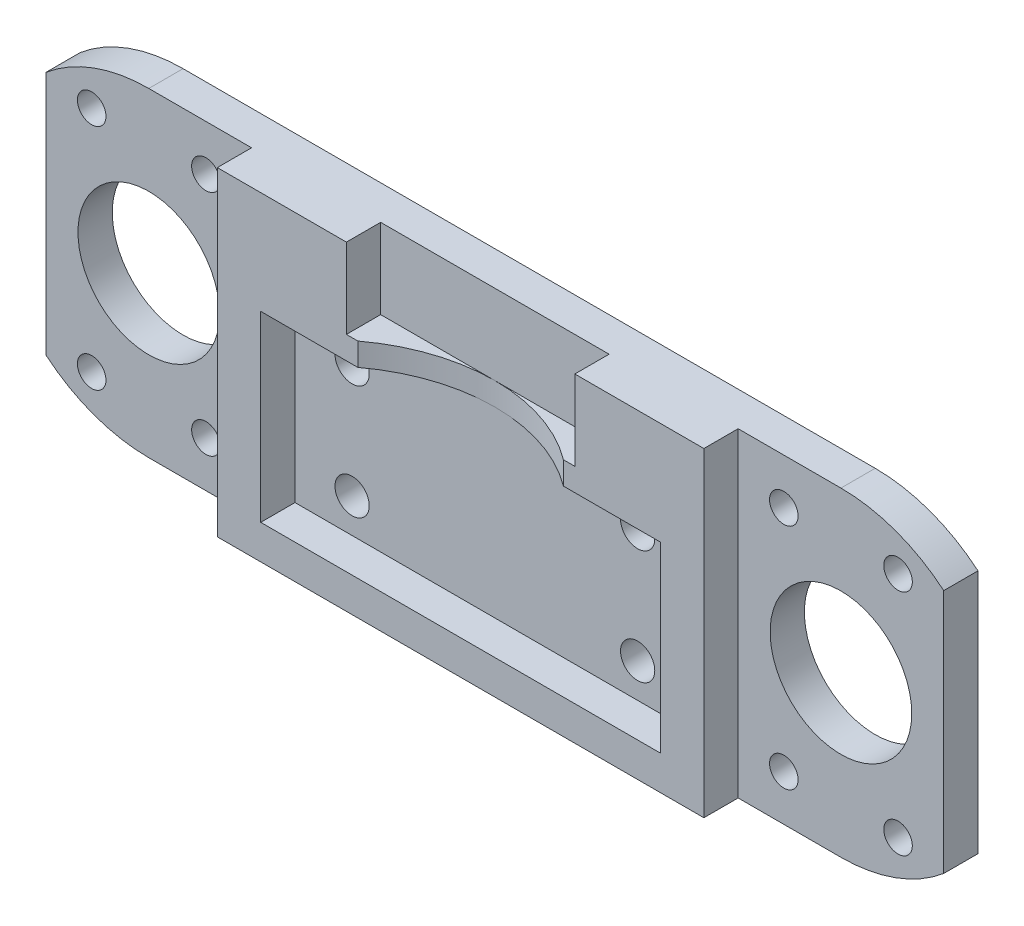
SolidWorks part; units mm, degrees
ref_plane "Front Plane" through (0, 0, 0) normal (0, 0, 1) x (1, 0, 0)
ref_plane "Top Plane" through (0, 0, 0) normal (0, 1, 0) x (1, 0, 0)
ref_plane "Right Plane" through (0, 0, 0) normal (1, 0, 0) x (0, 0, -1)
sketch "Sketch1" plane through (0, 0, 0) normal (0, 0, 1) x (1, 0, 0)
  line L0 (-39.3, 10.7238) -> (-39.3, -10.7238)
  line L1 (-30.3, -14) -> (30.3, -14)
  line L3 (-35.3, 10) -> (-25.3, -10) construction
  line L4 (-35.3, -10) -> (-25.3, 10) construction
  line L5 (-30.3, 14) -> (30.3, 14)
  line L6 (-30.3, 0) -> (30.3, 0) construction
  line L7 (39.3, 10.7238) -> (39.3, -10.7238)
  line L8 (25.3, 10) -> (35.3, -10) construction
  line L9 (35.3, 10) -> (25.3, -10) construction
  arc A0 (-30.3, 14) -> (-39.3, 10.7238) centre (-30.3, 0) ccw
  arc A1 (-39.3, -10.7238) -> (-30.3, -14) centre (-30.3, 0) ccw
  circle A2 centre (-30.3, 0) radius 6.2
  circle A3 centre (-35.3, 10) radius 1.25
  circle A4 centre (-25.3, 10) radius 1.25
  circle A5 centre (-35.3, -10) radius 1.25
  circle A6 centre (-25.3, -10) radius 1.25
  arc A7 (30.3, -14) -> (39.3, -10.7238) centre (30.3, 0) ccw
  arc A8 (39.3, 10.7238) -> (30.3, 14) centre (30.3, 0) ccw
  circle A9 centre (30.3, 0) radius 6.2
  circle A10 centre (25.3, 10) radius 1.25
  circle A11 centre (35.3, 10) radius 1.25
  circle A12 centre (25.3, -10) radius 1.25
  circle A13 centre (35.3, -10) radius 1.25
  point P7 (0, 0)
  point P8 (0, 0)
  point P18 (-30.3, 0)
  point P25 (30.3, 0)
  point P36 (30.3, 0)
  dimension "D2" = 14
  dimension "D3" = 12.4
  dimension "D6" = 2.5
  dimension "D8" = 2.5
  dimension "D11" = 28
  dimension "D4" = 20
  dimension "D5" = 10
  dimension "D7" = 60.6
  dimension "D9" = 10
  dimension "D10" = 20
  dimension "D16" = 9
extrude "Main" add sketch "Sketch1" along normal mid plane 3
sketch "Sketch2" plane through (0, 0, 1.5) normal (0, 0, -1) x (-1, 0, 0)
  line L0 (30.3, -14) -> (-30.3, -14) construction
  line L1 (39.3, 10.7238) -> (39.3, -10.7238) construction
  line L2 (21.3, 14) -> (10, 14)
  line L3 (21.3, 14) -> (21.3, -14)
  line L4 (21.3, -14) -> (-21.3, -14)
  line L5 (-21.3, 14) -> (-21.3, -14)
  line L6 (17.5, 5) -> (-17.5, 5)
  line L7 (17.5, 5) -> (17.5, -11)
  line L8 (17.5, -11) -> (-17.5, -11)
  line L9 (-17.5, 5) -> (-17.5, -11)
  line L10 (-39.3, -10.7238) -> (-39.3, 10.7238) construction
  line L11 (-30.3, 14) -> (30.3, 14) construction
  line L12 (-39.3, -10.7238) -> (-39.3, 10.7238) construction
  line L13 (-30.3, 14) -> (30.3, 14) construction
  line L14 (10, 14) -> (10, 7)
  line L15 (10, 7) -> (-10, 7)
  line L16 (-10, 7) -> (-10, 14)
  line L17 (-10, 14) -> (-21.3, 14)
  point P14 (0, 7)
  point P22 (0, 5)
  point P27 (17.5, -3)
  dimension "D1" = 16
  dimension "D2" = 3.8
  dimension "D3" = 18
  dimension "D4" = 7
  dimension "D5" = 35
  dimension "D6" = 78.6
  dimension "D7" = 18
  dimension "D8" = 3.8
  dimension "D9" = 3
  dimension "D10" = 2
  dimension "D11" = 20
  dimension "D12" = 3
  dimension "D13" = 35
extrude "Framework" add sketch "Sketch2" against normal blind 3
sketch "Sketch3" plane through (0, 0, -1.5) normal (0, 0, -1) x (-1, 0, 0)
  line L6 (17.5, 5) -> (17.5, -11) construction
  line L9 (17.5, -11) -> (-17.5, -11) construction
  circle A1 centre (12.5, -8) radius 1.5
  point P0 (17.5, -3)
  dimension "D1" = 3
  dimension "D2" = 5
  dimension "D3" = 12.5
  dimension "D4" = 8
  dimension "D5" = 5
  dimension "D6" = 3
extrude "FixHole" cut sketch "Sketch3" against normal through all
pattern_linear "HolePattern" count 2 spacing 25 along (1, 0, 0) count 2 spacing 10 along (0, 1, 0) of "FixHole"
sketch "Sketch4" plane through (0, 7, 0) normal (0, 1, 0) x (1, 0, 0)
  line L0 (-10, -1.5) -> (10, -1.5) construction
  circle A0 centre (0, -16.5) radius 15
  point P4 (0, 0)
  point P5 (0, 0)
  dimension "D1" = 30
extrude "Cut-Extrude1" cut sketch "Sketch4" against normal up to next
